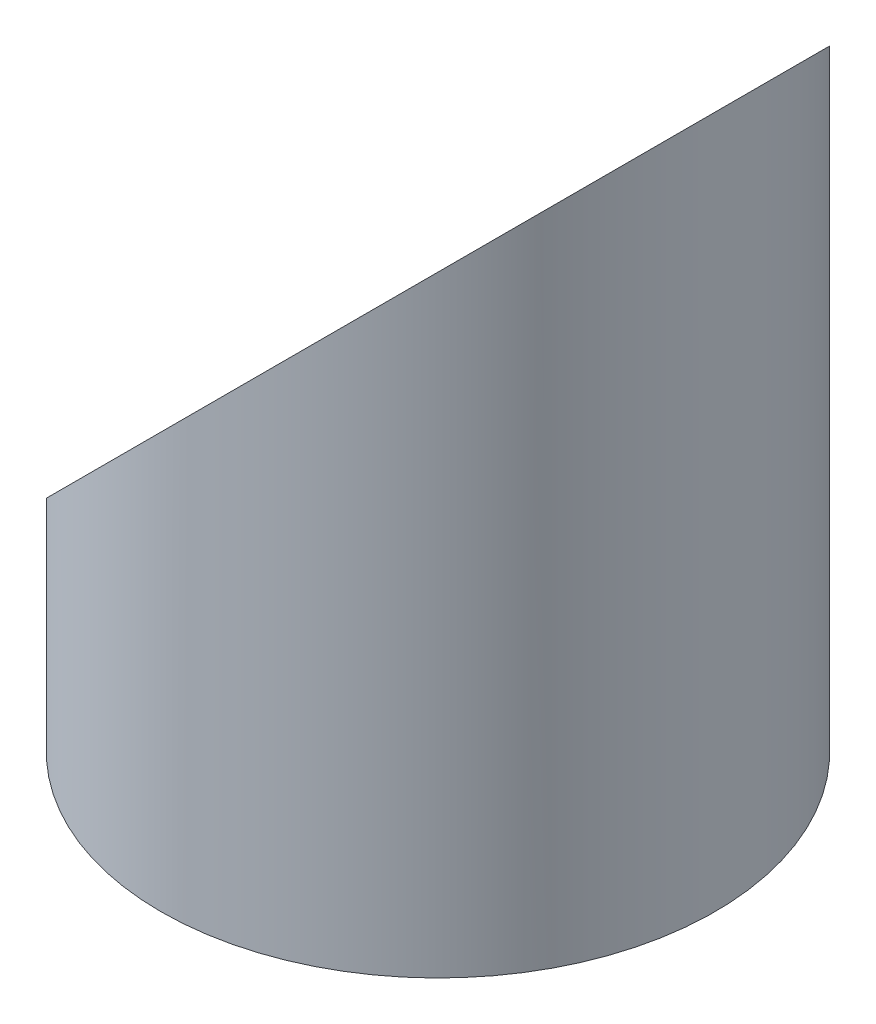
SolidWorks part; units mm, degrees
ref_plane "Front Plane" through (0, 0, 0) normal (0, 0, 1) x (1, 0, 0)
ref_plane "Top Plane" through (0, 0, 0) normal (0, 1, 0) x (1, 0, 0)
ref_plane "Right Plane" through (0, 0, 0) normal (1, 0, 0) x (0, 0, -1)
sketch "Sketch1" plane through (0, 0, 0) normal (0, 1, 0) x (1, 0, 0)
  line L0 (0, -20) -> (-20, 0)
  line L1 (0, -20) -> (20, 0)
  line L2 (-20, 0) -> (0, 20)
  line L3 (20, 0) -> (0, 20)
  circle A0 centre (0, 0) radius 40
  dimension "D1" = 80
  dimension "D2" = 20
  dimension "D3" = 40
  dimension "D4" = 20
  dimension "D5" = 20
  dimension "D6" = 90
  dimension "D7" = 20
extrude "Boss-Extrude1" add sketch "Sketch1" along normal blind 100
sketch "Sketch2" plane through (0, 0, 0) normal (0, 0, 1) x (1, 0, 0)
  line L0 (-40, 20) -> (40, 100)
  line L1 (-40, 100) -> (-40, 0) construction
  line L2 (40, 100) -> (-40, 100)
  line L3 (-40, 100) -> (-40, 20)
  dimension "D1" = 80
extrude "Cut-Extrude1" cut sketch "Sketch2" against normal through all and the other way through all
